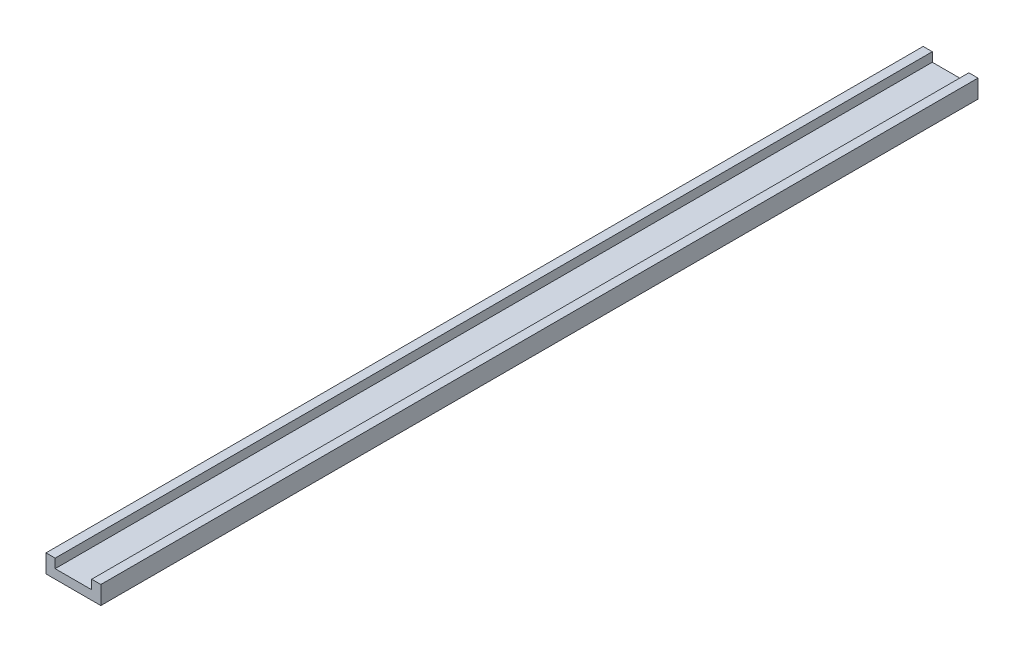
SolidWorks part; units mm, degrees
ref_plane "Front Plane" through (0, 0, 0) normal (0, 0, 1) x (1, 0, 0)
ref_plane "Top Plane" through (0, 0, 0) normal (0, 1, 0) x (1, 0, 0)
ref_plane "Right Plane" through (0, 0, 0) normal (1, 0, 0) x (0, 0, -1)
sketch "Sketch1" plane through (0, 0, 0) normal (0, 0, 1) x (1, 0, 0)
  line L1 (0, 0) -> (19.05, 0)
  line L2 (0, 0) -> (0, 6.35)
  line L3 (0, 6.35) -> (19.05, 6.35)
  line L4 (19.05, 0) -> (19.05, 6.35)
  dimension "D1" = 19.05
  dimension "D2" = 6.35
extrude "Boss-Extrude1" add sketch "Sketch1" along normal blind 304.8
sketch "Sketch2" plane through (0, 0, 304.8) normal (0, 0, 1) x (1, 0, 0)
  line L0 (19.05, 6.35) -> (0, 6.35) construction
  line L1 (3.175, 6.35) -> (15.875, 6.35)
  line L2 (3.175, 6.35) -> (3.175, 3.175)
  line L3 (3.175, 3.175) -> (15.875, 3.175)
  line L4 (15.875, 6.35) -> (15.875, 3.175)
  line L5 (0, 6.35) -> (0, 0) construction
  line L6 (19.05, 0) -> (19.05, 6.35) construction
  line L7 (0, 0) -> (19.05, 0) construction
  dimension "D1" = 3.175
  dimension "D2" = 3.175
  dimension "D3" = 3.175
extrude "Cut-Extrude1" cut sketch "Sketch2" against normal blind 304.8
